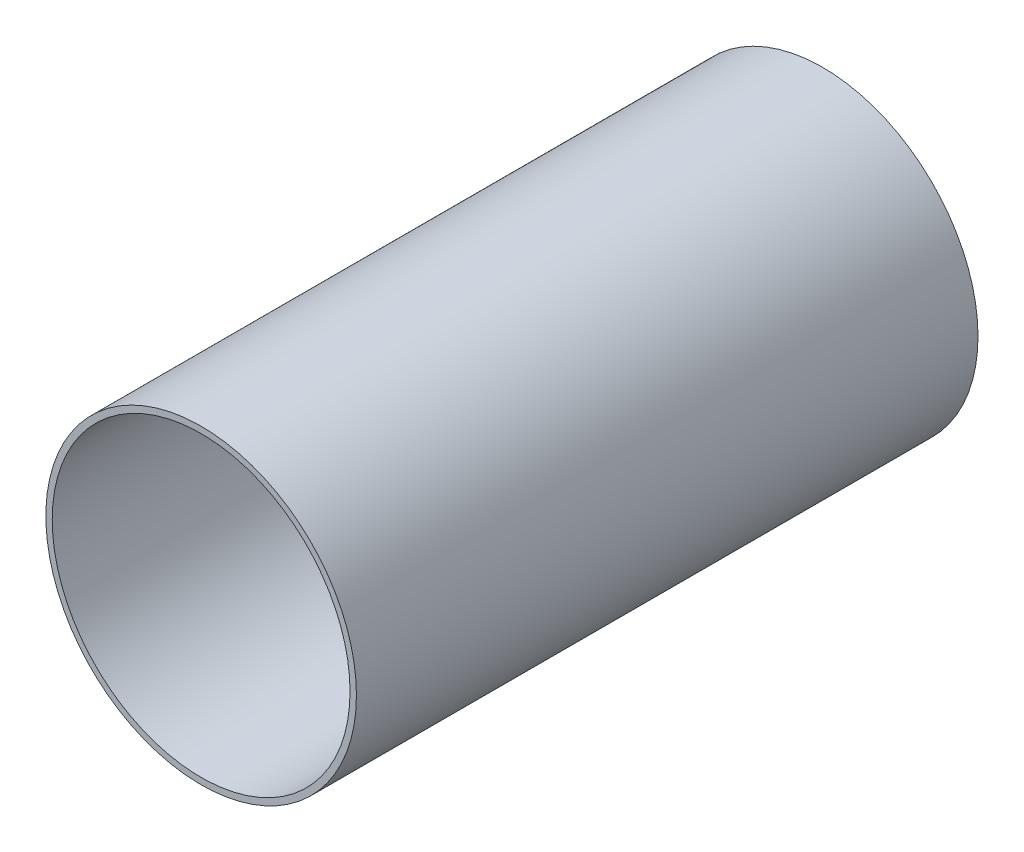
SolidWorks part; units mm, degrees
ref_plane "Front Plane" through (0, 0, 0) normal (0, 0, 1) x (1, 0, 0)
ref_plane "Top Plane" through (0, 0, 0) normal (0, 1, 0) x (1, 0, 0)
ref_plane "Right Plane" through (0, 0, 0) normal (1, 0, 0) x (0, 0, -1)
sketch "Sketch1" plane through (0, 0, 0) normal (0, 0, 1) x (1, 0, 0)
  circle A0 centre (0, 0) radius 38.0746
  circle A1 centre (0, 0) radius 36.5125
  dimension "D1" = 73.025
  dimension "D2" = 76.1492
extrude "Boss-Extrude1" add sketch "Sketch1" along normal mid plane 152.4
equation "\"AIRFRAME_OD\"= 3.142in"
equation "\"AIRFRAME_ID\"= 3.00in"
equation "\"FLAT_T\"= 0.125in"
equation "\"NOSE_EXP_L\"= 3.5in"
equation "\"NOSE_SHOULDER_L\"= 5in"
equation "\"MAIN_L\"= 30in"
equation "\"RECO_COUP_L\"= 6in"
equation "\"RECO_SWITCH_L\"= 1.5in"
equation "\"DROGUE_L\"= 14in"
equation "\"ATS_FORE_COUP_L\"= 4in"
equation "\"ATS_AFT_COUP_L\"= 2.5in"
equation "\"LOWER_L\"= 16in"
equation "\"FIN_N\"= 4"
equation "\"CR_AFT_X\"= 0.5in"
equation "\"CR_FORE_X\"= 6in"
equation "\"D1@Sketch1\"=\"COUPLER_ID\""
equation "\"D2@Sketch1\"=\"COUPLER_OD\""
equation "\"D1@Boss-Extrude1\"=\"RECO_COUP_L\""
equation "\"FIN_ROOT\"= 5in"
equation "\"FIN_X\"= 0.75in"
equation "\"MOTOR_OD\"= 2.25in"
equation "\"MOTOR_ID\"= 2.126in"
equation "\"COUPLER_OD\"= 2.998in"
equation "\"COUPLER_ID\"= 2.875in"
